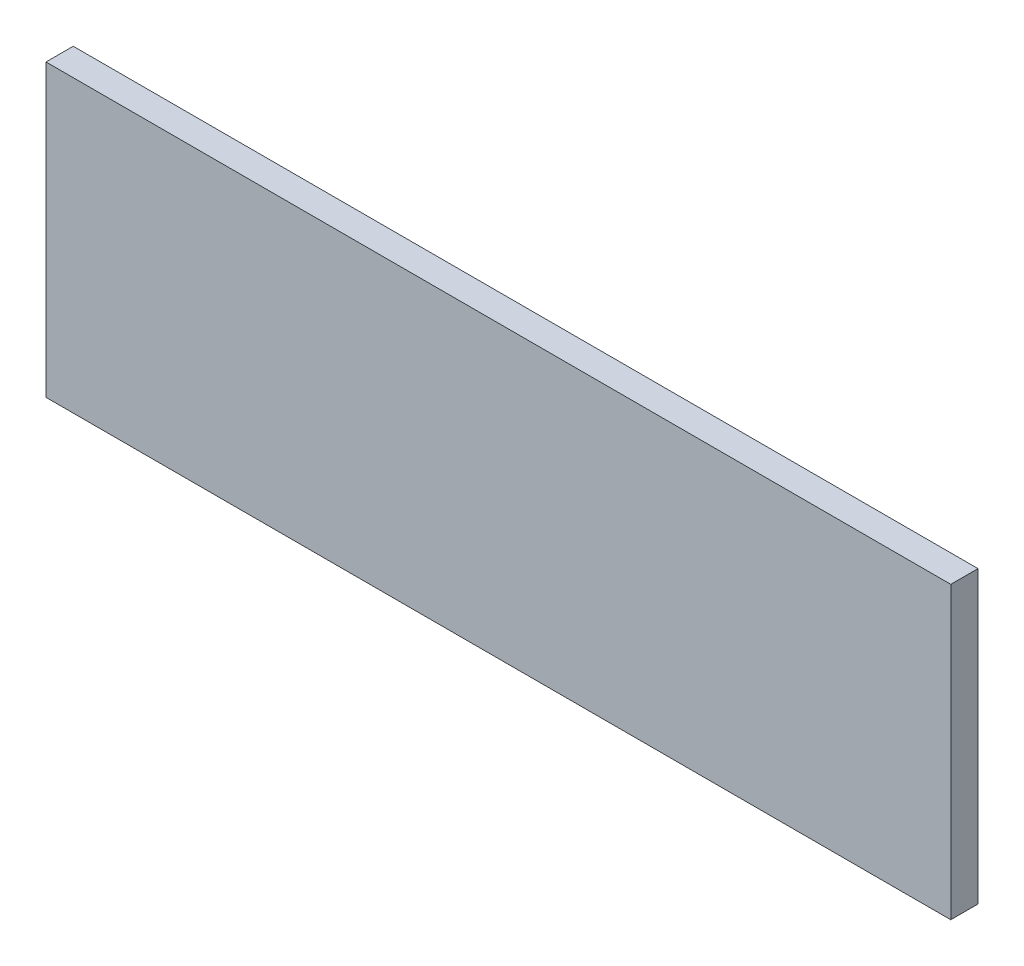
SolidWorks part; units mm, degrees
ref_plane "Front Plane" through (0, 0, 0) normal (0, 0, 1) x (1, 0, 0)
ref_plane "Top Plane" through (0, 0, 0) normal (0, 1, 0) x (1, 0, 0)
ref_plane "Right Plane" through (0, 0, 0) normal (1, 0, 0) x (0, 0, -1)
sketch "Sketch1" plane through (0, 0, 0) normal (0, 0, 1) x (1, 0, 0)
  line L1 (299, -96) -> (-299, -96)
  line L2 (299, -96) -> (299, 96)
  line L3 (299, 96) -> (-299, 96)
  line L4 (-299, -96) -> (-299, 96)
  line L5 (299, -96) -> (-299, 96) construction
  line L6 (299, 96) -> (-299, -96) construction
  point P0 (0, 0)
  dimension "D1" = 192
  dimension "D2" = 598
extrude "Boss-Extrude1" add sketch "Sketch1" along normal blind 18
equation "\"H_DSP\"=18"
equation "\"D1@Boss-Extrude1\"=\"H_DSP\""
